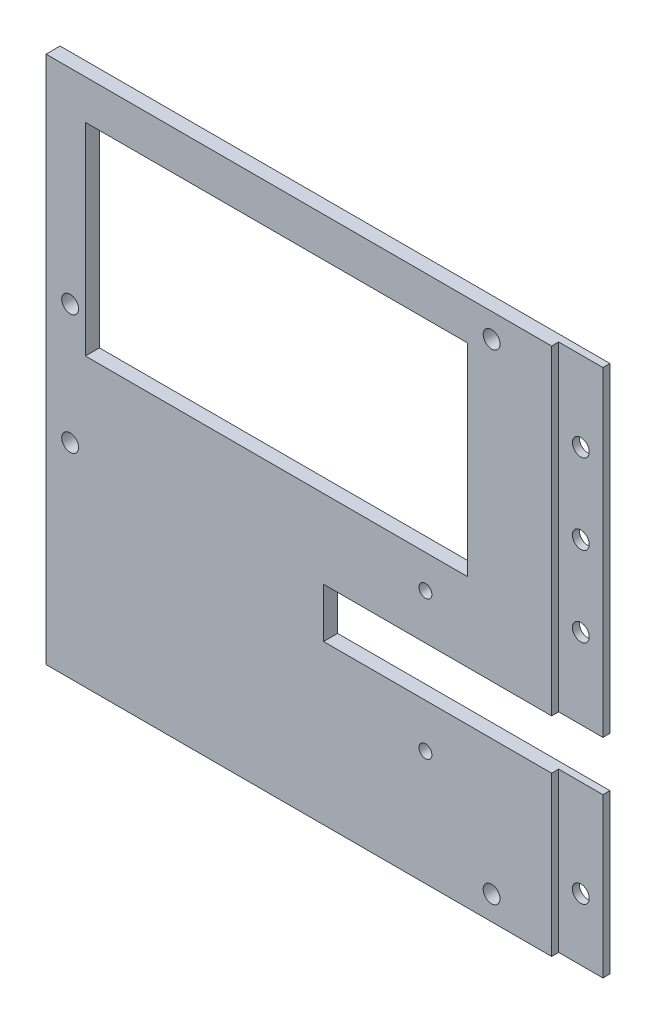
SolidWorks part; units mm, degrees
ref_plane "Front Plane" through (0, 0, 0) normal (0, 0, 1) x (1, 0, 0)
ref_plane "Top Plane" through (0, 0, 0) normal (0, 1, 0) x (1, 0, 0)
ref_plane "Right Plane" through (0, 0, 0) normal (1, 0, 0) x (0, 0, -1)
sketch "Sketch2" plane through (0, 0, 0) normal (0, 0, 1) x (1, 0, 0)
  line L1 (-21.3193, 8.8196) -> (102.8537, 8.8196)
  line L2 (-21.3193, 8.8196) -> (-21.3193, -110.5604)
  line L3 (-21.3193, -110.5604) -> (102.8537, -110.5604)
  line L4 (102.8537, 8.8196) -> (102.8537, -110.5604)
  dimension "D1" = 124.173
  dimension "D2" = 119.38
extrude "Boss-Extrude1" add sketch "Sketch2" along normal blind 3.175
sketch "Sketch4" plane through (0, 0, 0) normal (0, 0, 1) x (1, 0, 0)
  line L6 (-12.4293, -0.0704) -> (73.8707, -0.0704)
  line L7 (-12.4293, -0.0704) -> (-12.4293, -45.7704)
  line L8 (-12.4293, -45.7704) -> (73.8707, -45.7704)
  line L9 (73.8707, -0.0704) -> (73.8707, -45.7704)
  line L10 (-21.3193, -110.5604) -> (102.8537, -110.5604) construction
  line L11 (102.8537, -110.5604) -> (102.8537, 8.8196) construction
  line L12 (41.3537, -63.5134) -> (102.8537, -63.5134)
  line L13 (41.3537, -63.5134) -> (41.3537, -74.7134)
  line L14 (41.3537, -74.7134) -> (102.8537, -74.7134)
  line L15 (102.8537, -63.5134) -> (102.8537, -74.7134)
  circle A0 centre (-15.8673, -37.3204) radius 1.905
  circle A1 centre (-15.8673, -64.4224) radius 1.905
  circle A2 centre (79.3027, 3.3676) radius 1.905
  circle A3 centre (79.3007, -105.1084) radius 1.905
  circle A4 centre (64.3537, -53.2994) radius 1.46
  circle A5 centre (64.3537, -84.6494) radius 1.46
  dimension "D5" = 61.5
  dimension "D2" = 10.214
  dimension "D4" = 23.551
  dimension "D3" = 9.936
  dimension "D6" = 27.102
  dimension "D8" = 5.452
  dimension "D9" = 35.847
  dimension "D10" = 25.911
extrude "Cut-Extrude1" cut sketch "Sketch4" along normal blind 14.175
sketch "Sketch10" plane through (102.8537, 0, 0) normal (1, 0, 0) x (0, 0, -1)
  line L1 (-3.175, 8.8196) -> (-1.585, 8.8196)
  line L2 (-3.175, 8.8196) -> (-3.175, -111.1804)
  line L3 (-3.175, -111.1804) -> (-1.585, -111.1804)
  line L4 (-1.585, 8.8196) -> (-1.585, -111.1804)
  dimension "D1" = 1.59
  dimension "D2" = 120
extrude "Cut-Extrude3" cut sketch "Sketch10" against normal blind 10
sketch "Sketch11" plane through (0, 0, 3.175) normal (0, 0, 1) x (1, 0, 0)
  line L1 (102.8537, -63.5134) -> (102.8537, 8.8196) construction
  line L2 (102.8537, -110.5604) -> (102.8537, -74.7134) construction
  line L3 (92.8537, 8.8196) -> (102.8537, 8.8196) construction
  line L4 (92.8537, -63.5134) -> (102.8537, -63.5134) construction
  circle A0 centre (97.8537, -9.2629) radius 1.905
  circle A1 centre (97.8537, -27.3454) radius 1.905
  circle A2 centre (97.8537, -45.4309) radius 1.905
  circle A3 centre (97.8537, -96.5604) radius 1.905
  point P10 (0, 0)
  dimension "D1" = 5
  dimension "D2" = 5
  dimension "D3" = 5
  dimension "D4" = 5
  dimension "D6" = 36.165
  dimension "D7" = 18.0825
  dimension "D8" = 18.0825
extrude "Cut-Extrude4" cut sketch "Sketch11" against normal blind 10
